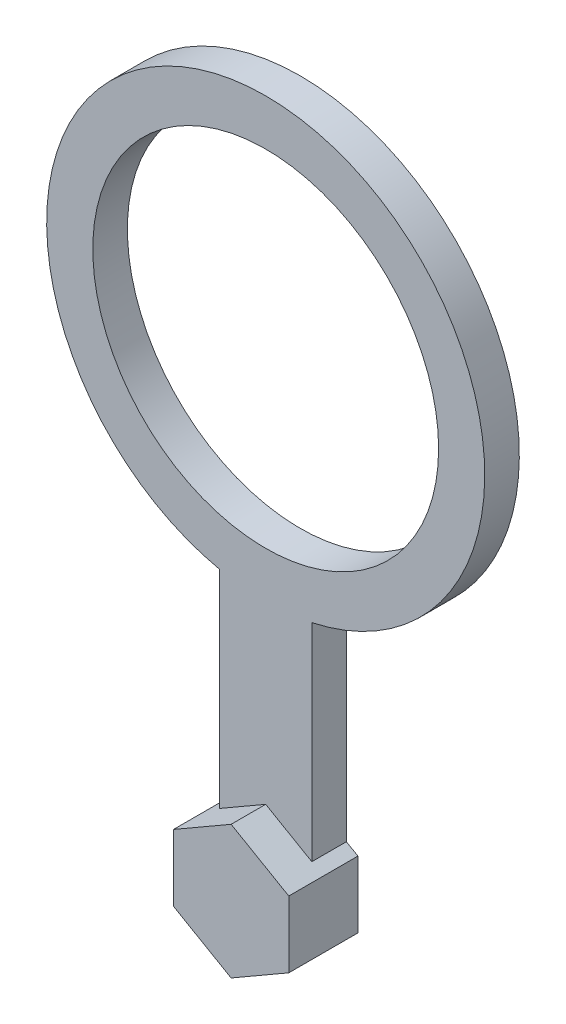
SolidWorks part; units mm, degrees
ref_plane "Front Plane" through (0, 0, 0) normal (0, 0, 1) x (1, 0, 0)
ref_plane "Top Plane" through (0, 0, 0) normal (0, 1, 0) x (1, 0, 0)
ref_plane "Right Plane" through (0, 0, 0) normal (1, 0, 0) x (0, 0, -1)
sketch "Sketch1" plane through (0, 0, 0) normal (0, 0, 1) x (1, 0, 0)
  line L0 (0, 0) -> (0, 40) construction
  line L1 (0, 5.7735) -> (-5, 2.8868)
  line L2 (-5, 2.8868) -> (-5, -2.8868)
  line L3 (-5, -2.8868) -> (0, -5.7735)
  line L4 (0, -5.7735) -> (5, -2.8868)
  line L5 (5, -2.8868) -> (5, 2.8868)
  line L6 (5, 2.8868) -> (0, 5.7735)
  line L7 (-4, 3.4641) -> (-4, 21.4258)
  line L8 (4, 3.4641) -> (4, 21.4258)
  line L9 (4, 3.4641) -> (-4, 3.4641) construction
  circle A0 centre (0, 0) radius 5 construction
  circle A1 centre (0, 40) radius 15
  circle A2 centre (0, 40) radius 19
  point P1 (5, 0)
  dimension "D2" = 30
  dimension "D3" = 4
  dimension "D1" = 10
  dimension "D4" = 8
  dimension "D5" = 40
extrude "Boss-Extrude1" add sketch "Sketch1" along normal blind 3 contours L5 L6 L1 L2 L3 L4 | A2 L7 L1 L6 L8 | A2 A1
sketch "Sketch2" plane through (0, 0, 3) normal (0, 0, 1) x (1, 0, 0)
  line L1 (0, -5.7735) -> (5, -2.8868)
  line L2 (5, -2.8868) -> (5, 2.8868)
  line L3 (5, 2.8868) -> (0, 5.7735)
  line L4 (0, 5.7735) -> (-5, 2.8868)
  line L5 (-5, 2.8868) -> (-5, -2.8868)
  line L6 (-5, -2.8868) -> (0, -5.7735)
  circle A0 centre (0, 0) radius 5 construction
  point P1 (1.0796, 5.11)
  point P10 (0, 0)
extrude "Boss-Extrude2" add sketch "Sketch2" along normal blind 3
